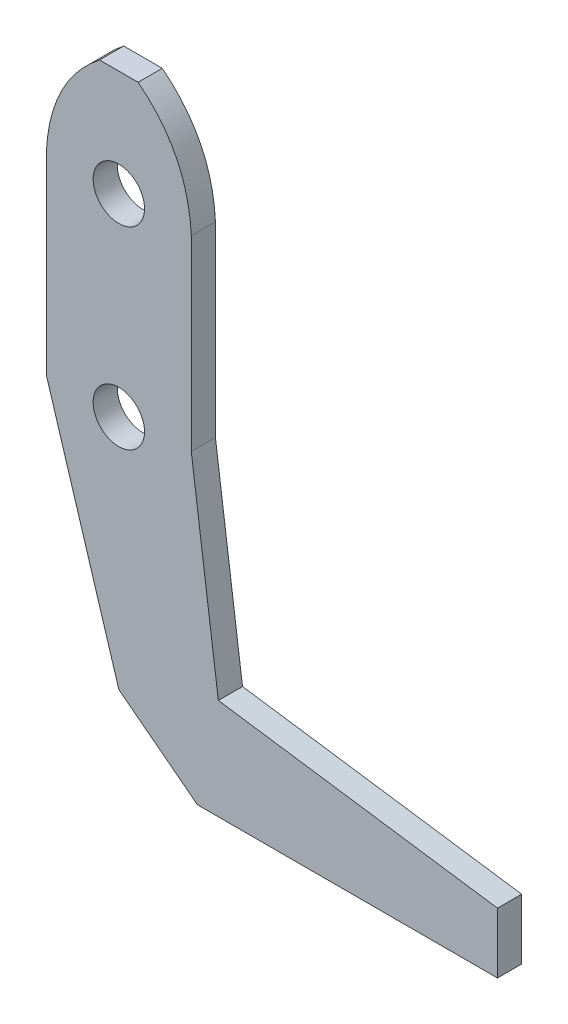
SolidWorks part; units mm, degrees
ref_plane "Front Plane" through (0, 0, 0) normal (0, 0, 1) x (1, 0, 0)
ref_plane "Top Plane" through (0, 0, 0) normal (0, 1, 0) x (1, 0, 0)
ref_plane "Right Plane" through (0, 0, 0) normal (1, 0, 0) x (0, 0, -1)
sketch "Sketch1" plane through (0, 0, 0) normal (0, 0, 1) x (1, 0, 0)
  line L0 (-2.54, 39.37) -> (2.54, 39.37)
  line L14 (10.327, -38.9756) -> (49.7728, -38.9756)
  line L17 (-9.525, 0) -> (0, -31.0256)
  line L18 (0, -31.0256) -> (10.327, -38.9756)
  line L19 (49.7728, -38.9756) -> (49.7728, -31.0256)
  line L20 (49.7728, -31.0256) -> (13.0807, -25.7257)
  line L21 (13.0807, -25.7257) -> (9.525, 0.8331)
  line L23 (-9.525, 25.4) -> (-9.525, 0)
  line L25 (9.525, 25.4) -> (9.525, 0.8331)
  line L26 (-9.525, 25.4) -> (9.525, 25.4) construction
  line L27 (0, -55) -> (0, 55) construction
  circle A0 centre (0, 25.4) radius 3.3782
  circle A1 centre (0, 0) radius 3.3782
  spline S0 degree 2 poles (-2.54, 39.37) (-9.0954, 34.2016) (-9.525, 25.4) knots 0 0 0 1 1 1
  spline S1 degree 2 poles (2.54, 39.37) (9.0954, 34.2016) (9.525, 25.4) knots 0 0 0 1 1 1
  point P6 (0, 39.37)
  point P7 (-6.3157, 35.398)
  point P20 (0, 25.4)
  point P21 (0, 39.37)
  dimension "D1" = 6.7564
  dimension "D7" = 5.08
  dimension "D2" = 25.4
  dimension "D3" = 39.37
  dimension "D6" = 19.05
extrude "Boss-Extrude1" add sketch "Sketch1" along normal blind 3.175
